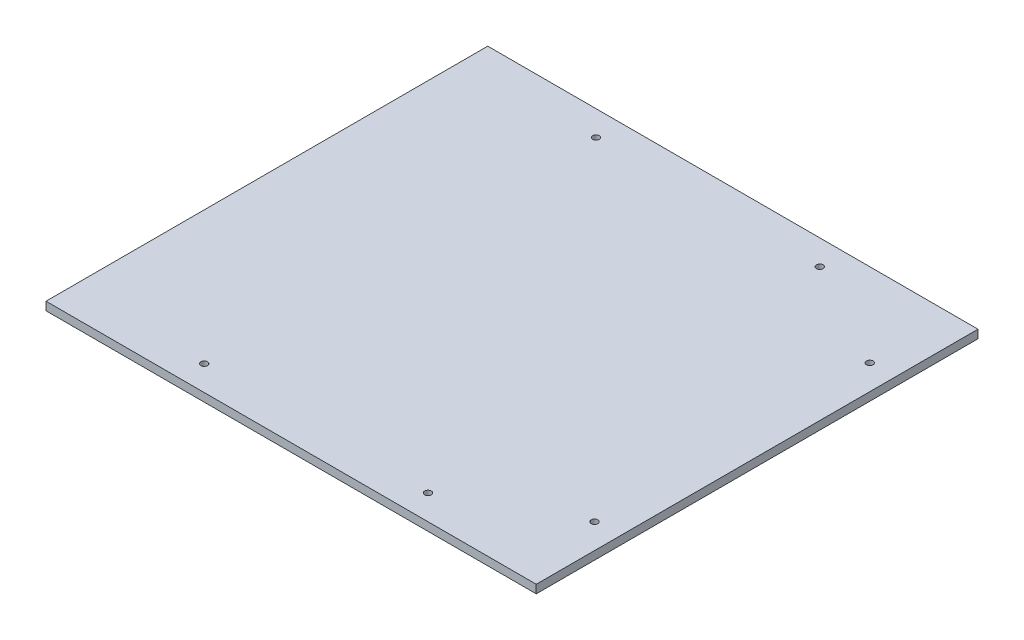
SolidWorks part; units mm, degrees
ref_plane "Front Plane" through (0, 0, 0) normal (0, 0, 1) x (1, 0, 0)
ref_plane "Top Plane" through (0, 0, 0) normal (0, 1, 0) x (1, 0, 0)
ref_plane "Right Plane" through (0, 0, 0) normal (1, 0, 0) x (0, 0, -1)
sketch "Sketch1" plane through (0, 0, 0) normal (0, 1, 0) x (1, 0, 0)
  line L1 (-147.2, 132.64) -> (147.2, 132.64)
  line L2 (-147.2, 132.64) -> (-147.2, -132.64)
  line L3 (-147.2, -132.64) -> (147.2, -132.64)
  line L4 (147.2, 132.64) -> (147.2, -132.64)
  point P4 (0, 132.64)
  point P6 (147.2, 0)
  dimension "D1" = 265.28
  dimension "D2" = 294.4
extrude "Boss-Extrude1" add sketch "Sketch1" along normal blind 5
sketch "Sketch2" plane through (0, 5, 0) normal (0, 1, 0) x (1, 0, 0)
  line L0 (132.2, -157.2095) -> (132.2, 196.3729) construction
  line L6 (147.2, -132.64) -> (147.2, 132.64) construction
  line L7 (-147.2, -132.64) -> (147.2, -132.64) construction
  line L8 (147.2, 132.64) -> (-147.2, 132.64) construction
  circle A4 centre (132.2, -82.64) radius 2
  circle A5 centre (132.2, 82.64) radius 2
  dimension "D2" = 50
  dimension "D1" = 15
  dimension "D3" = 4
  dimension "D4" = 50
extrude "Cut-Extrude1" cut sketch "Sketch2" against normal blind 5
sketch "Sketch3" plane through (0, 5, 0) normal (0, 1, 0) x (1, 0, 0)
  line L0 (-175.4272, 0) -> (196.7765, 0) construction
  line L1 (-167.7736, 117.64) -> (171.399, 117.64) construction
  line L2 (147.2, 132.64) -> (-147.2, 132.64) construction
  line L5 (147.2, -132.64) -> (147.2, 132.64) construction
  line L6 (-147.2, 132.64) -> (-147.2, -132.64) construction
  circle A0 centre (-67.2, 117.64) radius 2
  circle A1 centre (67.2, 117.64) radius 2
  circle A2 centre (67.2, -117.64) radius 2
  circle A3 centre (-67.2, -117.64) radius 2
  dimension "D2" = 4
  dimension "D1" = 15
  dimension "D3" = 80
  dimension "D4" = 80
extrude "Cut-Extrude2" cut sketch "Sketch3" against normal blind 5
